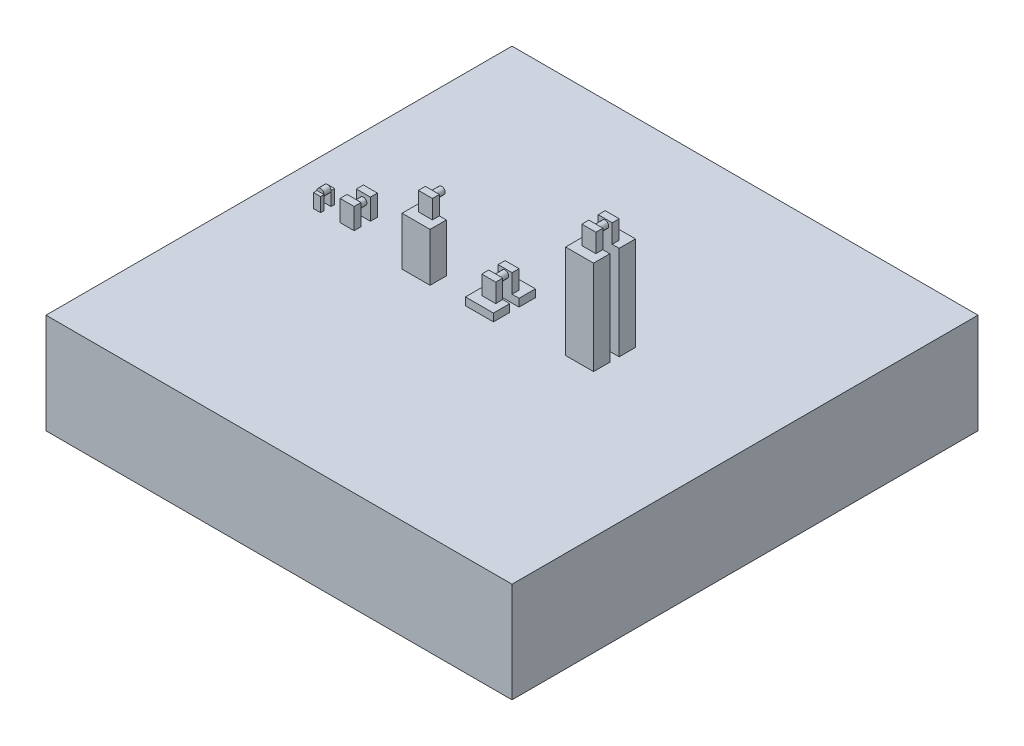
SolidWorks part; units mm, degrees
ref_plane "前基準面" through (0, 0, 0) normal (0, 0, 1) x (1, 0, 0)
ref_plane "上基準面" through (0, 0, 0) normal (0, 1, 0) x (1, 0, 0)
ref_plane "右基準面" through (0, 0, 0) normal (1, 0, 0) x (0, 0, -1)
sketch "草圖1" plane through (0, 0, 0) normal (0, 1, 0) x (1, 0, 0)
  line L1 (-50, 50) -> (50, 50)
  line L2 (-50, 50) -> (-50, -50)
  line L3 (-50, -50) -> (50, -50)
  line L4 (50, 50) -> (50, -50)
  line L5 (-50, 50) -> (50, -50) construction
  line L6 (-50, -50) -> (50, 50) construction
  point P0 (0, 0)
  dimension "D1" = 100
  dimension "D2" = 100
extrude "填料-伸長1" add sketch "草圖1" along normal blind 1.5 and the other way blind 20
sketch "草圖2" plane through (0, 0, 0) normal (0, 0, 1) x (1, 0, 0)
  line L0 (-50, 1.5) -> (50, 1.5) construction
  circle A0 centre (-40.3368, 4.5) radius 0.75
  dimension "D1" = 1.5
  dimension "D2" = 3
extrude "填料-伸長2" add sketch "草圖2" along normal mid plane 1.5 separate body
sketch "草圖3" plane through (0, 0, 0.75) normal (0, 0, 1) x (1, 0, 0)
  line L0 (-50, 1.5) -> (50, 1.5) construction
  line L1 (-41.0868, 4.5) -> (-39.5868, 4.5)
  line L2 (-41.0868, 4.5) -> (-41.0868, 1.5)
  line L3 (-41.0868, 1.5) -> (-39.5868, 1.5)
  line L4 (-39.5868, 4.5) -> (-39.5868, 1.5)
  circle A0 centre (-40.3368, 4.5) radius 0.75 construction
  dimension "D2" = 0.75
  dimension "D1" = 1.5
  dimension "D3" = 3
extrude "填料-伸長3" add sketch "草圖3" along normal blind 1.5
mirror "鏡射1" about plane through (0, 0, 0) normal (0, 0, 1) of "填料-伸長3"
sketch "草圖5" plane through (0, 4.5, 0) normal (0, 1, 0) x (1, 0, 0)
  line L1 (-35.6368, 0.25) -> (-32.6368, 0.25)
  line L2 (-35.6368, 0.25) -> (-35.6368, -1.25)
  line L3 (-35.6368, -1.25) -> (-32.6368, -1.25)
  line L4 (-32.6368, 0.25) -> (-32.6368, -1.25)
  line L9 (-35.6368, 2.25) -> (-32.6368, 2.25)
  line L10 (-35.6368, 2.25) -> (-35.6368, 3.75)
  line L11 (-35.6368, 3.75) -> (-32.6368, 3.75)
  line L12 (-32.6368, 2.25) -> (-32.6368, 3.75)
  dimension "D3" = 1.5
  dimension "D4" = 3
  dimension "D5" = 1.5
  dimension "D6" = 3
  dimension "D7" = 2
extrude "填料-伸長4" add sketch "草圖5" against normal up to surface (3 mm away) up to face at (-40.3368, 1.5, -1.5)
sketch "草圖7" plane through (0, 0, -2.25) normal (0, 0, 1) x (1, 0, 0)
  line L0 (-35.6368, 1.5) -> (-35.6368, 4.5) construction
  line L1 (-32.6368, 1.5) -> (-35.6368, 1.5) construction
  circle A0 centre (-34.1368, 4.5) radius 0.75
  dimension "D1" = 1.5
  dimension "D2" = 1.5
  dimension "D3" = 3
extrude "填料-伸長5" add sketch "草圖7" along normal blind 2.5
sketch "草圖8" plane through (0, 1.5, 0) normal (0, 1, 0) x (1, 0, 0)
  line L0 (-32.6368, 3.75) -> (-35.6368, 3.75) construction
  line L1 (-20.3368, 5.75) -> (-14.3368, 5.75)
  line L2 (-20.3368, 5.75) -> (-20.3368, -3.25)
  line L3 (-20.3368, -3.25) -> (-14.3368, -3.25)
  line L4 (-14.3368, 5.75) -> (-14.3368, -3.25)
  line L5 (-20.3368, 5.75) -> (-14.3368, -3.25) construction
  line L6 (-20.3368, -3.25) -> (-14.3368, 5.75) construction
  line L7 (-35.6368, 2.25) -> (-34.8868, 2.25) construction
  line L8 (-35.6368, 3.75) -> (-32.6368, 3.75) construction
  point P0 (-17.3368, 1.25)
  point P7 (-34.1368, 3.75)
  dimension "D1" = 16.8
  dimension "D2" = 6
  dimension "D3" = 1
  dimension "D4" = 2
extrude "填料-伸長6" add sketch "草圖8" along normal blind 10.4
sketch "草圖9" plane through (0, 11.9, 0) normal (0, 1, 0) x (1, 0, 0)
  line L0 (-32.6368, 3.75) -> (-35.6368, 3.75) construction
  line L1 (-18.8368, 3.75) -> (-15.8368, 3.75)
  line L2 (-18.8368, 3.75) -> (-18.8368, 2.25)
  line L3 (-18.8368, 2.25) -> (-15.8368, 2.25)
  line L4 (-15.8368, 3.75) -> (-15.8368, 2.25)
  line L5 (-35.6368, 2.25) -> (-35.6368, 3.75) construction
  line L6 (-22.4008, 1.25) -> (-12.2755, 1.25) construction
  line L7 (-15.8368, -1.25) -> (-15.8368, 0.25)
  line L8 (-18.8368, 0.25) -> (-15.8368, 0.25)
  line L9 (-18.8368, -1.25) -> (-18.8368, 0.25)
  line L10 (-18.8368, -1.25) -> (-15.8368, -1.25)
  point P8 (-35.6368, 3)
  dimension "D1" = 1.5
  dimension "D2" = 3
  dimension "D3" = 16.8
  dimension "D4" = 1
extrude "填料-伸長7" add sketch "草圖9" along normal blind 4
sketch "草圖10" plane through (0, 0, -2.25) normal (0, 0, 1) x (1, 0, 0)
  line L0 (-20.3368, 11.9) -> (-14.3368, 11.9) construction
  line L1 (-18.8368, 15.9) -> (-18.8368, 11.9) construction
  circle A0 centre (-17.3368, 14.9) radius 0.75
  dimension "D1" = 1.5
  dimension "D2" = 3
  dimension "D3" = 1.5
extrude "填料-伸長8" add sketch "草圖10" along normal blind 3
sketch "草圖11" plane through (0, 11.9, 0) normal (0, 1, 0) x (1, 0, 0)
  line L0 (-20.3368, 5.75) -> (-20.3368, -3.25) construction
  line L1 (-20.3368, 2.25) -> (-14.3368, 2.25)
  line L2 (-20.3368, 2.25) -> (-20.3368, 0.25)
  line L3 (-20.3368, 0.25) -> (-14.3368, 0.25)
  line L4 (-14.3368, 2.25) -> (-14.3368, 0.25)
  line L5 (-14.3368, -3.25) -> (-14.3368, 5.75) construction
  line L6 (-15.8368, 0.25) -> (-18.8368, 0.25) construction
  line L7 (-18.8368, 2.25) -> (-15.8368, 2.25) construction
extrude "除料-伸長1" cut sketch "草圖11" against normal up to surface (10.4 mm away) up to face at (-34.1368, 1.5, -3)
sketch "草圖12" plane through (0, 1.5, 0) normal (0, 1, 0) x (1, 0, 0)
  line L1 (13.2432, 1.75) -> (19.2432, 1.75)
  line L2 (13.2432, 1.75) -> (13.2432, -1.75)
  line L3 (13.2432, -1.75) -> (19.2432, -1.75)
  line L4 (19.2432, 1.75) -> (19.2432, -1.75)
  line L5 (-14.3368, 0.25) -> (-20.3368, 0.25) construction
  line L7 (-20.3368, 0.25) -> (-20.3368, -3.25) construction
  line L8 (11.5568, 2.75) -> (25.799, 2.75) construction
  line L9 (19.2432, 3.75) -> (19.2432, 7.25)
  line L10 (13.2432, 7.25) -> (19.2432, 7.25)
  line L11 (13.2432, 3.75) -> (13.2432, 7.25)
  line L12 (13.2432, 3.75) -> (19.2432, 3.75)
  dimension "D1" = 3.5
  dimension "D2" = 1.5
  dimension "D3" = 6
  dimension "D4" = 33.58
  dimension "D5" = 1
extrude "填料-伸長9" add sketch "草圖12" along normal blind 20.17
sketch "草圖13" plane through (0, 21.67, 0) normal (0, 1, 0) x (1, 0, 0)
  line L0 (19.2432, 1.75) -> (13.2432, 1.75) construction
  line L1 (14.7432, 1.75) -> (17.7432, 1.75)
  line L2 (14.7432, 1.75) -> (14.7432, 0.25)
  line L3 (14.7432, 0.25) -> (17.7432, 0.25)
  line L4 (17.7432, 1.75) -> (17.7432, 0.25)
  line L8 (19.2432, -1.75) -> (19.2432, 1.75) construction
  line L9 (13.2432, 1.75) -> (13.2432, -1.75) construction
  line L10 (11.5568, 2.75) -> (25.799, 2.75) construction
  line L11 (11.5568, 2.75) -> (25.799, 2.75) construction
  line L12 (17.7432, 3.75) -> (17.7432, 5.25)
  line L13 (14.7432, 5.25) -> (17.7432, 5.25)
  line L14 (14.7432, 3.75) -> (14.7432, 5.25)
  line L15 (14.7432, 3.75) -> (17.7432, 3.75)
  dimension "D1" = 1.5
  dimension "D2" = 1.5
  dimension "D3" = 1.5
extrude "填料-伸長10" add sketch "草圖13" along normal blind 4
sketch "草圖14" plane through (0, 0, -3.75) normal (0, 0, 1) x (1, 0, 0)
  line L0 (14.7432, 25.67) -> (14.7432, 21.67) construction
  line L1 (13.2432, 21.67) -> (19.2432, 21.67) construction
  circle A0 centre (16.2432, 24.67) radius 0.75
  dimension "D1" = 1.5
  dimension "D2" = 1.5
  dimension "D3" = 3
extrude "填料-伸長11" add sketch "草圖14" along normal up to surface (2 mm away) up to face at (16.2432, 17.6275, -1.75)
pattern_linear "直線複製排列2" count 2 spacing 13.6 along (1, 0, 0) of "填料-伸長6"
sketch "草圖16" plane through (0, 0, 0) normal (0, 0, 1) x (1, 0, 0)
  line L0 (-6.7368, 11.9) -> (-6.7368, 1.5) construction
  line L1 (-6.7368, 3.15) -> (-0.7368, 3.15)
  line L2 (-6.7368, 3.15) -> (-6.7368, 11.9)
  line L3 (-6.7368, 11.9) -> (-0.7368, 11.9)
  line L4 (-0.7368, 3.15) -> (-0.7368, 11.9)
  line L5 (-6.7368, 1.5) -> (-0.7368, 1.5) construction
  dimension "D1" = 1.65
extrude "除料-伸長2" cut sketch "草圖16" against normal mid plane 18.5
sketch "草圖17" plane through (0, 3.15, 0) normal (0, 1, 0) x (1, 0, 0)
  line L0 (-6.7368, 2.25) -> (-0.7368, 2.25)
  line L1 (-6.7368, 0.25) -> (-0.7368, 0.25)
  line L2 (-0.7368, -3.25) -> (-0.7368, 5.75) construction
  line L3 (-6.7368, 5.75) -> (-6.7368, -3.25) construction
  line L4 (-0.7368, 0.25) -> (-0.7368, 2.25)
  line L5 (-6.7368, 2.25) -> (-6.7368, 0.25)
  line L6 (-6.7368, 5.75) -> (-0.7368, 5.75) construction
  dimension "D1" = 2
  dimension "D2" = 3.5
extrude "除料-伸長3" cut sketch "草圖17" against normal up to surface (1.65 mm away) up to face at (-17.3368, 1.5, 1.5)
sketch "草圖18" plane through (0, 3.15, 0) normal (0, 1, 0) x (1, 0, 0)
  line L0 (-6.7368, 2.25) -> (-0.7368, 2.25) construction
  line L1 (-5.2368, 2.25) -> (-2.2368, 2.25)
  line L2 (-5.2368, 2.25) -> (-5.2368, 3.75)
  line L3 (-5.2368, 3.75) -> (-2.2368, 3.75)
  line L4 (-2.2368, 2.25) -> (-2.2368, 3.75)
  line L5 (-0.7368, 5.75) -> (-0.7368, 2.25) construction
  line L7 (-6.7368, 0.25) -> (-0.7368, 0.25) construction
  line L8 (-5.2368, 0.25) -> (-2.2368, 0.25)
  line L9 (-5.2368, 0.25) -> (-5.2368, -1.25)
  line L10 (-5.2368, -1.25) -> (-2.2368, -1.25)
  line L11 (-2.2368, 0.25) -> (-2.2368, -1.25)
  dimension "D1" = 3
  dimension "D2" = 1.5
  dimension "D3" = 1.5
  dimension "D4" = 1.5
extrude "填料-伸長12" add sketch "草圖18" along normal blind 4
sketch "草圖19" plane through (0, 0, -2.25) normal (0, 0, 1) x (1, 0, 0)
  line L0 (-5.2368, 3.15) -> (-2.2368, 3.15) construction
  line L1 (-5.2368, 7.15) -> (-5.2368, 3.15) construction
  circle A0 centre (-3.7368, 6.15) radius 0.75
  dimension "D1" = 1.5
  dimension "D2" = 3
  dimension "D3" = 1.5
extrude "填料-伸長13" add sketch "草圖19" along normal blind 3
sketch "草圖20" plane through (0, 4.5, 0) normal (0, 1, 0) x (1, 0, 0)
  line L0 (-32.6368, 0.25) -> (-33.3868, 0.25) construction
  line L1 (-33.3868, 0.25) -> (-33.3868, -0.25) construction
  line L2 (-33.3868, -0.25) -> (-34.8868, -0.25) construction
  line L3 (-34.8868, -0.25) -> (-34.8868, 0.25) construction
  line L4 (-34.8868, 0.25) -> (-35.6368, 0.25) construction
  line L5 (-35.6368, 0.25) -> (-35.6368, -1.25) construction
  line L6 (-35.6368, -1.25) -> (-32.6368, -1.25) construction
  line L7 (-32.6368, -1.25) -> (-32.6368, 0.25) construction
  line L8 (-35.6368, 3.75) -> (-35.6368, 2.25) construction
  line L9 (-35.6368, 2.25) -> (-34.8868, 2.25) construction
  line L10 (-34.8868, 2.25) -> (-33.3868, 2.25) construction
  line L11 (-33.3868, 2.25) -> (-32.6368, 2.25) construction
  line L12 (-32.6368, 2.25) -> (-32.6368, 3.75) construction
  line L13 (-32.6368, 3.75) -> (-35.6368, 3.75) construction
  line L14 (-32.6368, 0.25) -> (-33.3868, 0.25)
  line L15 (-33.3868, 0.25) -> (-33.3868, -0.25)
  line L16 (-33.3868, -0.25) -> (-34.8868, -0.25)
  line L17 (-34.8868, -0.25) -> (-34.8868, 0.25)
  line L18 (-34.8868, 0.25) -> (-35.6368, 0.25)
  line L19 (-35.6368, 0.25) -> (-35.6368, -1.25)
  line L20 (-35.6368, -1.25) -> (-32.6368, -1.25)
  line L21 (-32.6368, -1.25) -> (-32.6368, 0.25)
  line L22 (-35.6368, 3.75) -> (-35.6368, 2.25)
  line L23 (-35.6368, 2.25) -> (-34.8868, 2.25)
  line L24 (-34.8868, 2.25) -> (-33.3868, 2.25)
  line L25 (-33.3868, 2.25) -> (-32.6368, 2.25)
  line L26 (-32.6368, 2.25) -> (-32.6368, 3.75)
  line L27 (-32.6368, 3.75) -> (-35.6368, 3.75)
extrude "填料-伸長14" add sketch "草圖20" along normal blind 1.5
sketch "草圖21" plane through (-41.0868, 0, 0) normal (-1, 0, 0) x (0, 0, 1)
  line L0 (2.25, 1.5) -> (0.75, 1.5) construction
  line L1 (1.5, 1.5) -> (2.25, 1.5)
  line L2 (1.5, 1.5) -> (1.5, 4.5)
  line L3 (1.5, 4.5) -> (2.25, 4.5)
  line L4 (2.25, 1.5) -> (2.25, 4.5)
  line L5 (-2.25, 1.5) -> (-0.75, 1.5) construction
  line L6 (-1.5, 1.5) -> (-2.25, 1.5)
  line L7 (-1.5, 1.5) -> (-1.5, 4.5)
  line L8 (-1.5, 4.5) -> (-2.25, 4.5)
  line L9 (-2.25, 1.5) -> (-2.25, 4.5)
extrude "除料-伸長4" cut sketch "草圖21" against normal blind 1.5
sketch "草圖22" plane through (0, 6, 0) normal (0, 1, 0) x (1, 0, 0)
  line L1 (-34.8868, 0.25) -> (-33.3868, 0.25)
  line L2 (-34.8868, 0.25) -> (-34.8868, -0.25)
  line L3 (-34.8868, -0.25) -> (-33.3868, -0.25)
  line L4 (-33.3868, 0.25) -> (-33.3868, -0.25)
extrude "填料-伸長15" add sketch "草圖22" against normal blind 2.5
sketch "草圖23" plane through (-20.3368, 0, 0) normal (-1, 0, 0) x (0, 0, 1)
  line L1 (-5.75, 1.5) -> (-2.25, 1.5)
  line L2 (-5.75, 1.5) -> (-5.75, 15.9)
  line L3 (-5.75, 15.9) -> (-2.25, 15.9)
  line L4 (-2.25, 1.5) -> (-2.25, 15.9)
extrude "除料-伸長5" cut sketch "草圖23" against normal up to surface (6 mm away) up to face at (-14.3368, 6.7, -4)
